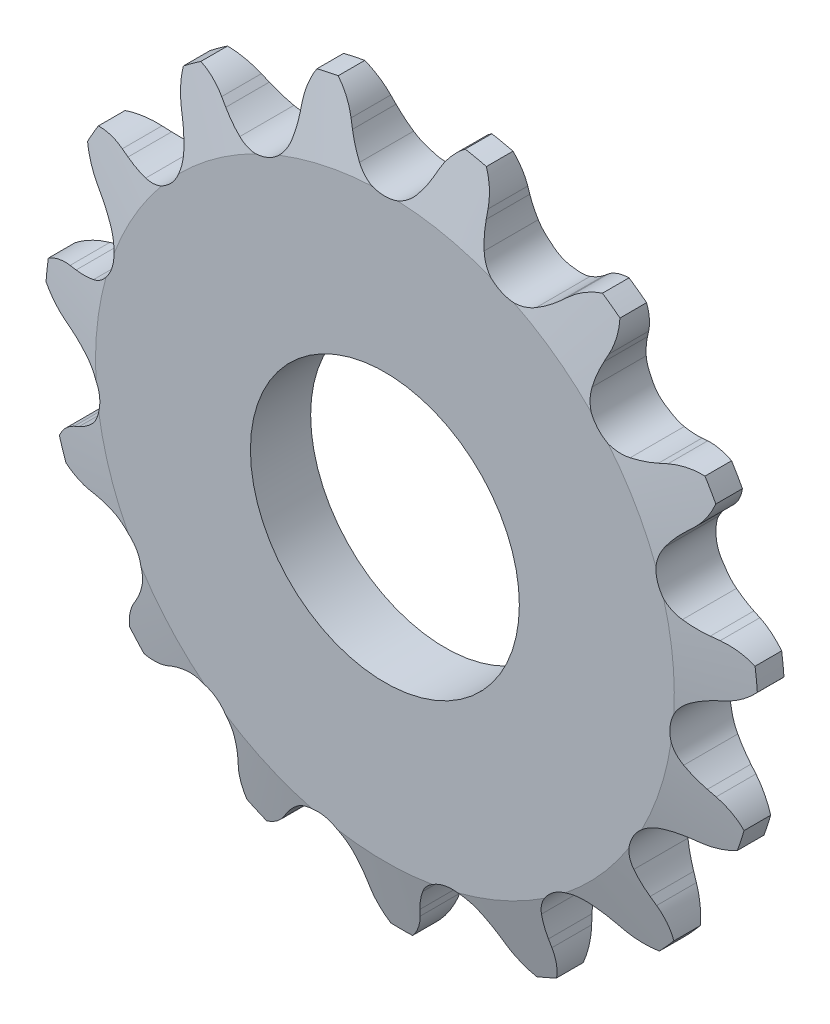
SolidWorks part; units mm, degrees
ref_plane "Front Plane" through (0, 0, 0) normal (0, 0, 1) x (1, 0, 0)
ref_plane "Top Plane" through (0, 0, 0) normal (0, 1, 0) x (1, 0, 0)
ref_plane "Right Plane" through (0, 0, 0) normal (1, 0, 0) x (0, 0, -1)
sketch "Sketch0" plane through (0, 0, 0) normal (0, 0, 1) x (1, 0, 0)
  line L0 (4.7625, -22.4058) -> (0, 0) construction
  line L1 (0, 0) -> (13.464, -18.5316) construction
  line L2 (0, 0) -> (-4.7625, -22.4058) construction
  line L3 (4.7625, -22.4058) -> (13.464, -18.5316) construction
  line L4 (4.7625, -22.4058) -> (-4.7625, -22.4058) construction
  line L5 (7.8768, -22.0376) -> (7.5383, -21.5839)
  line L6 (4.7625, -22.4058) -> (0, -23.4181) construction
  line L7 (1.7676, -23.3362) -> (1.8924, -22.784)
  line L8 (0, -22.4058) -> (0, -25.2633) construction
  line L9 (6.3929, -20.3924) -> (2.2049, -25.5641) construction
  line L10 (0, 0) -> (0, -22.4058) construction
  line L11 (7.5383, -21.5839) -> (2.2049, -25.5641) construction
  line L12 (0, -25.2633) -> (0, -25.9124) construction
  line L13 (11.2596, -19.5131) -> (7.8768, -22.0376) construction
  circle A0 centre (0, 0) radius 25.2633 construction
  circle A1 centre (0, 0) radius 22.9064 construction
  arc A2 (-2.7897, -26.6037) -> (13.3692, -23.1691) centre (0, 0) ccw
  circle A3 centre (0, 0) radius 25.9124 construction
  circle A4 centre (4.7625, -22.4058) radius 2.54 construction
  arc A7 (6.3929, -20.3924) -> (2.4541, -21.2296) centre (4.7625, -22.4058) ccw
  circle A8 centre (4.7625, -22.4058) radius 2.5908 construction
  arc A9 (7.8768, -22.0376) -> (13.3692, -23.1691) centre (11.2596, -19.5131) ccw
  arc A10 (7.5383, -21.5839) -> (6.3929, -20.3924) centre (2.2049, -25.5641) ccw
  arc A11 (1.7676, -23.3362) -> (-2.7897, -26.6037) centre (-2.3495, -22.4058) cw
  arc A12 (1.8924, -22.784) -> (2.4541, -21.2296) centre (8.3836, -24.2508) cw
  dimension "D1" = 2.5908
  dimension "R" = 2.5908
sketch "Sketch1" plane through (0, 0, 0) normal (1, 0, 0) x (0, 0, -1)
  line L0 (2.1336, 0) -> (-2.1336, 0)
  line L1 (-2.1336, 0) -> (-2.1336, 20.5008)
  line L2 (-2.1336, 20.5008) -> (-0.943, 25.2633)
  line L3 (-0.943, 25.2633) -> (0.943, 25.2633)
  line L4 (0.943, 25.2633) -> (2.1336, 20.5008)
  line L5 (2.1336, 20.5008) -> (2.1336, 0)
  line L7 (0, 25.2633) -> (0, 0) construction
  line L8 (-2.1336, 20.5008) -> (2.1336, 20.5008) construction
  line L9 (0, 25.2633) -> (0, -25.2633) construction
  line L10 (-2.1336, 20.5008) -> (-2.1336, 25.2633) construction
  line L11 (-2.1336, 25.2633) -> (-0.943, 25.2633) construction
  line L12 (0.943, 25.2633) -> (2.1336, 25.2633) construction
  line L13 (2.1336, 25.2633) -> (2.1336, 20.5008) construction
revolve "Revolve1" add sketch "Sketch1" angle 360 mid plane about L0
extrude "Cut-Extrude1" cut sketch "Sketch0" against normal through all and the other way through all
pattern_circular "CirPattern1" count 15 over 360 about axis through (0, 0, 0) along (0, 0, 1) of "Cut-Extrude1"
sketch "Sketch2" plane through (0, 0, 0) normal (0, 0, 1) x (1, 0, 0)
  circle A0 centre (0, 0) radius 6.35 construction
  circle A1 centre (0, 0) radius 30.1625
  circle A2 centre (0, 0) radius 25.273 construction
  dimension "Bore" = 12.7
  dimension "Hub Dia." = 60.325
  dimension "OD" = 50.546
sketch "Sketch3" plane through (0, 0, 0) normal (0, 0, 1) x (1, 0, 0)
  circle A0 centre (0, 0) radius 6.35 construction
  circle A1 centre (0, 0) radius 6.35
  circle A2 centre (0, 0) radius 25.273 construction
  circle A3 centre (0, 0) radius 25.273
extrude "Cut-Extrude2" cut sketch "Sketch3" along normal through all and the other way through all flip side to cut
sketch "Sketch4" plane through (0, 0, 2.1336) normal (0, 0, 1) x (1, 0, 0)
  circle A0 centre (0, 0) radius 9.525
  dimension "D1" = 19.05
extrude "Cut-Extrude3" cut sketch "Sketch4" against normal through all
equation "\"360/N@Sketch0\" = 360/\"Teeth@CirPattern1\""
equation "\"Ds@Sketch0\" = 1.005 * \"Dr@Sketch0\" + 0.003"
equation "\"R@Sketch0\" = 1/2 * \"Ds@Sketch0\""
equation "\"A@Sketch0\" = 35 +  ( 60 / \"Teeth@CirPattern1\" ) "
equation "\"B@Sketch0\" = 18 -  ( 56 / \"Teeth@CirPattern1\" )"
equation "\"ac@Sketch0\" = 0.8 * \"Dr@Sketch0\""
equation "\"ab@Sketch0\" = 1.4 * \"Dr@Sketch0\""
equation "\"J@Sketch0\" = 0.3 * \"Pitch@Sketch0\""
equation "\"h@Sketch1\" = \"Pitch@Sketch0\" / 2"
equation "\"g@Sketch1\" = \"h@Sketch1\" / 4"
